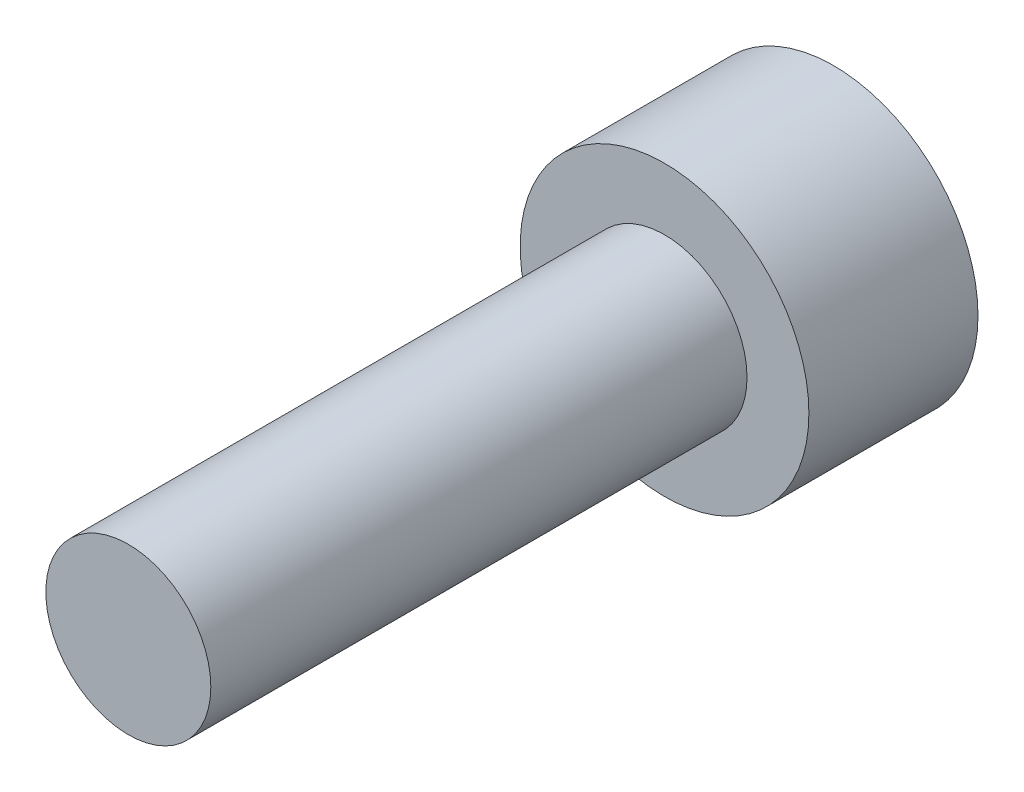
SolidWorks part; units mm, degrees
material "Commercially Pure CP-Ti UNS R50700  Grade 4 (SS)"
ref_plane "前视基准面" through (0, 0, 0) normal (0, 0, 1) x (1, 0, 0)
ref_plane "上视基准面" through (0, 0, 0) normal (0, 1, 0) x (1, 0, 0)
ref_plane "右视基准面" through (0, 0, 0) normal (1, 0, 0) x (0, 0, -1)
other "Configuration Table"
sketch "Sketch2" plane through (0, 0, 0) normal (0, 0, 1) x (1, 0, 0)
  circle A0 centre (0, 0) radius 3.5
  dimension "D1" = 7
extrude "Boss-Extrude1" add sketch "Sketch2" along normal blind 4.1 contours A0
sketch "Sketch3" plane through (0, 0, 4.1) normal (0, 0, 1) x (1, 0, 0)
  circle A0 centre (0, 0) radius 2
  dimension "D1" = 4
extrude "Boss-Extrude2" add sketch "Sketch3" along normal blind 13
cosmetic thread "Cosmetic Thread1" parameters "D1"=5, "D2"=3
